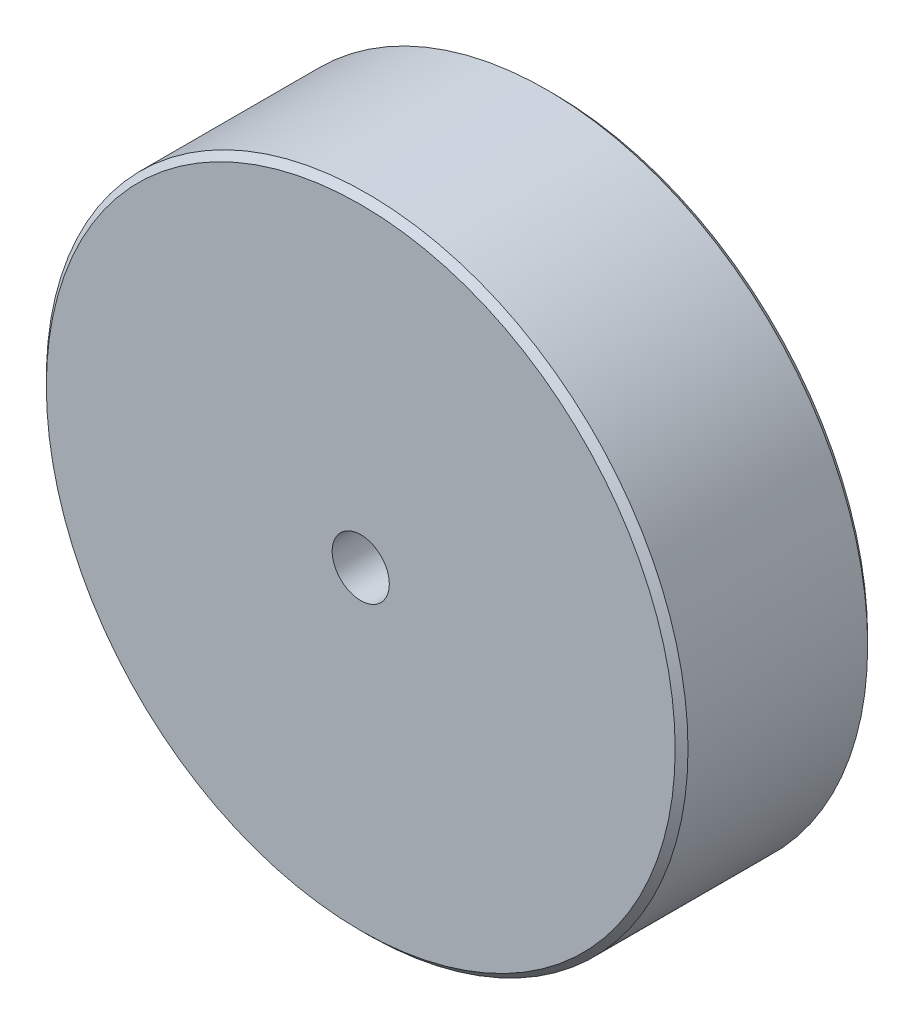
SolidWorks part; units mm, degrees
material "6061-T6 (SS)"
ref_plane "Front Plane" through (0, 0, 0) normal (0, 0, 1) x (1, 0, 0)
ref_plane "Top Plane" through (0, 0, 0) normal (0, 1, 0) x (1, 0, 0)
ref_plane "Right Plane" through (0, 0, 0) normal (1, 0, 0) x (0, 0, -1)
sketch "Sketch1" plane through (0, 0, 0) normal (0, 0, 1) x (1, 0, 0)
  circle A0 centre (0, 0) radius 12.7
  dimension "D1" = 25.4
extrude "Boss-Extrude1" add sketch "Sketch1" along normal blind 7.62
hole_wizard "#4-40 Tapped Hole1" positions "Sketch2" profile "Sketch3" tap size "#4-40" standard "ANSI Inch"
sketch "Sketch2" plane through (0, 0, 7.62) normal (0, 0, 1) x (1, 0, 0)
  point P0 (0, 0)
sketch "Sketch3" plane through (0, 0, 7.62) normal (1, 0, 0) x (0, -1, 0)
  line L0 (0, 0) -> (0, 6.35)
  line L1 (0, 6.35) -> (1.1303, 5.6708)
  line L2 (1.1303, 5.6708) -> (1.1303, 0)
  line L5 (1.1303, 0) -> (0, 0)
  line L10 (0, 6.35) -> (-1.1303, 5.6708) construction
  line L11 (0, -6.35) -> (0, 107.95) construction
  dimension "Tap Drill Dia." = 2.2606
  dimension "Tap Drill Depth" = 6.35
  dimension "Drill Angle" = 118
chamfer "Chamfer1" distance 0.254 angle 45 2 edges at (12.7, 0, 0) (12.7, 0, 7.62)
